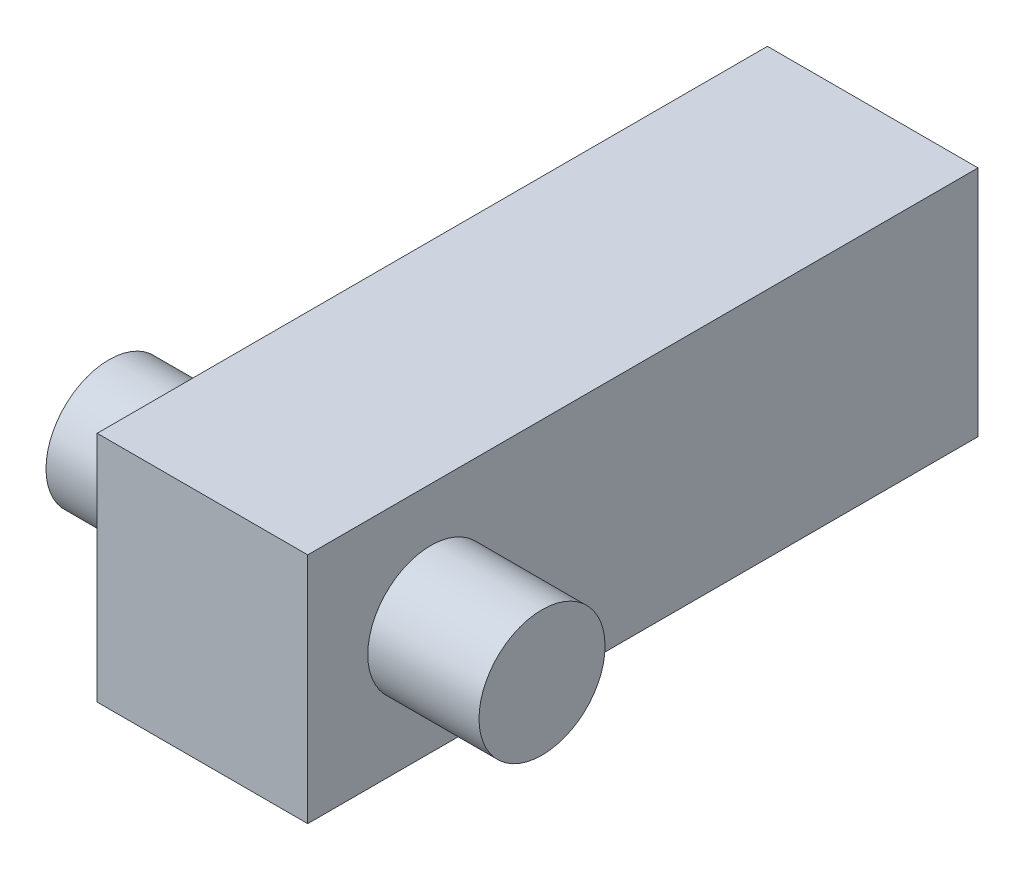
SolidWorks part; units mm, degrees
ref_plane "Front Plane" through (0, 0, 0) normal (0, 0, 1) x (1, 0, 0)
ref_plane "Top Plane" through (0, 0, 0) normal (0, 1, 0) x (1, 0, 0)
ref_plane "Right Plane" through (0, 0, 0) normal (1, 0, 0) x (0, 0, -1)
sketch "Sketch1" plane through (0, 0, 0) normal (0, 1, 0) x (1, 0, 0)
  line L1 (0, 0) -> (36.068, 0)
  line L2 (0, 0) -> (0, 114.808)
  line L3 (0, 114.808) -> (36.068, 114.808)
  line L4 (36.068, 0) -> (36.068, 114.808)
  dimension "D1" = 36.068
  dimension "D2" = 114.808
extrude "Boss-Extrude1" add sketch "Sketch1" along normal blind 39.878
sketch "Sketch3" plane through (0, 0, 0) normal (-1, 0, 0) x (0, 0, 1)
  circle A0 centre (-21.082, 19.939) radius 10.795
  dimension "D2" = 21.59
extrude "Boss-Extrude2" add sketch "Sketch3" along normal blind 19.05
sketch "Sketch4" plane through (36.068, 0, 0) normal (1, 0, 0) x (0, 0, -1)
  circle A0 centre (21.082, 19.939) radius 10.795 construction
  circle A1 centre (21.082, 19.939) radius 10.795
extrude "Boss-Extrude4" add sketch "Sketch4" along normal blind 19.05
